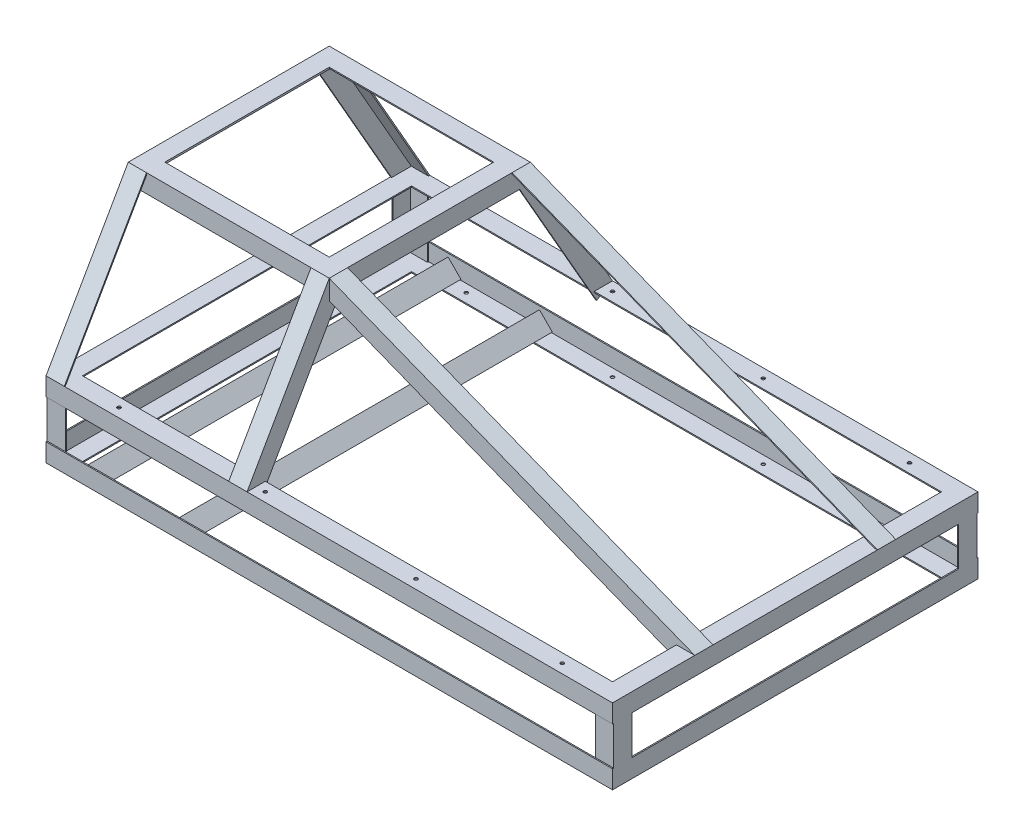
SolidWorks part; units mm, degrees
material "6061 Alloy"
ref_plane "Front Plane" through (0, 0, 0) normal (0, 0, 1) x (1, 0, 0)
ref_plane "Top Plane" through (0, 0, 0) normal (0, 1, 0) x (1, 0, 0)
ref_plane "Right Plane" through (0, 0, 0) normal (1, 0, 0) x (0, 0, -1)
sketch "Sketch2" plane through (0, 0, 0) normal (1, 0, 0) x (0, 0, -1)
  line L0 (-504.825, -346.075) -> (-504.825, -422.275)
  line L1 (504.825, -422.275) -> (-504.825, -422.275) construction
  line L2 (504.825, -422.275) -> (504.825, 422.275) construction
  line L3 (504.825, 422.275) -> (-504.825, 422.275) construction
  line L4 (-504.825, -422.275) -> (-504.825, 422.275) construction
  line L5 (504.825, -422.275) -> (-504.825, 422.275) construction
  line L6 (504.825, 422.275) -> (-504.825, -422.275) construction
  line L7 (-504.825, -422.275) -> (-428.625, -422.275)
  line L8 (-428.625, -422.275) -> (-428.625, -417.195)
  line L9 (-428.625, -417.195) -> (-498.7519, -417.195)
  line L10 (-498.7519, -417.195) -> (-498.7519, -346.075)
  line L11 (-498.7519, -346.075) -> (-504.825, -346.075)
  line L12 (0, 0) -> (0, -148.4726) construction
  line L13 (0, 0) -> (158.633, 0) construction
  line L14 (498.7519, -417.195) -> (498.7519, -346.075)
  line L15 (428.625, -417.195) -> (498.7519, -417.195)
  line L16 (428.625, -422.275) -> (428.625, -417.195)
  line L17 (504.825, -422.275) -> (428.625, -422.275)
  line L18 (504.825, -346.075) -> (504.825, -422.275)
  line L19 (498.7519, -346.075) -> (504.825, -346.075)
  line L20 (428.625, 417.195) -> (498.7519, 417.195)
  line L21 (428.625, 422.275) -> (428.625, 417.195)
  line L22 (504.825, 422.275) -> (428.625, 422.275)
  line L23 (504.825, 346.075) -> (504.825, 422.275)
  line L24 (498.7519, 346.075) -> (504.825, 346.075)
  line L25 (498.7519, 417.195) -> (498.7519, 346.075)
  line L26 (-498.7519, 417.195) -> (-498.7519, 346.075)
  line L27 (-428.625, 417.195) -> (-498.7519, 417.195)
  line L28 (-428.625, 422.275) -> (-428.625, 417.195)
  line L29 (-504.825, 422.275) -> (-428.625, 422.275)
  line L30 (-504.825, 346.075) -> (-504.825, 422.275)
  line L31 (-498.7519, 346.075) -> (-504.825, 346.075)
  point P0 (0, 0)
  dimension "D1" = 1009.65
  dimension "D2" = 844.55
  dimension "D3" = 76.2
  dimension "D4" = 5.08
extrude "OAL Lenth" [suppressed] add sketch "Sketch2" along normal blind 1574.8
sketch "Sketch3" [suppressed] plane through (0, 0, 0) normal (0, 0, 1) x (1, 0, 0)
  line L0 (0, -422.275) -> (0, -346.075)
  line L1 (1574.8, -346.075) -> (0, -346.075) construction
  line L2 (0, -346.075) -> (0, -422.275) construction
  line L3 (0, -346.075) -> (5.08, -346.075)
  line L4 (5.08, -346.075) -> (5.08, -417.195)
  line L5 (5.08, -417.195) -> (76.2, -417.195)
  line L6 (76.2, -417.195) -> (76.2, -422.275)
  line L7 (1574.8, -422.275) -> (0, -422.275) construction
  line L8 (76.2, -422.275) -> (0, -422.275)
  line L9 (0, 0) -> (697.1877, 0) construction
  line L10 (787.4, 346.075) -> (787.4, -346.075) construction
  line L11 (1574.8, 346.075) -> (0, 346.075) construction
  line L12 (76.2, 422.275) -> (0, 422.275)
  line L13 (76.2, 417.195) -> (76.2, 422.275)
  line L14 (5.08, 417.195) -> (76.2, 417.195)
  line L15 (5.08, 346.075) -> (5.08, 417.195)
  line L16 (0, 346.075) -> (5.08, 346.075)
  line L17 (0, 422.275) -> (0, 346.075)
  line L18 (1574.8, 422.275) -> (1574.8, 346.075)
  line L19 (1574.8, 346.075) -> (1569.72, 346.075)
  line L20 (1569.72, 346.075) -> (1569.72, 417.195)
  line L21 (1569.72, 417.195) -> (1498.6, 417.195)
  line L22 (1498.6, 417.195) -> (1498.6, 422.275)
  line L23 (1498.6, 422.275) -> (1574.8, 422.275)
  line L24 (1498.6, -422.275) -> (1574.8, -422.275)
  line L25 (1498.6, -417.195) -> (1498.6, -422.275)
  line L26 (1569.72, -417.195) -> (1498.6, -417.195)
  line L27 (1569.72, -346.075) -> (1569.72, -417.195)
  line L28 (1574.8, -346.075) -> (1569.72, -346.075)
  line L29 (1574.8, -422.275) -> (1574.8, -346.075)
  dimension "D1" = 5.08
extrude "OAL Width" [suppressed] add sketch "Sketch3" along normal up to surface and the other way up to surface
sketch "Sketch4" [suppressed] plane through (0, 422.275, 0) normal (0, 1, 0) x (1, 0, 0)
  line L0 (0, 504.825) -> (0, 428.625)
  line L1 (0, -428.625) -> (0, -504.825) construction
  line L2 (0, 428.625) -> (5.08, 428.625)
  line L3 (5.08, 428.625) -> (5.08, 499.745)
  line L4 (5.08, 499.745) -> (76.2, 499.745)
  line L5 (76.2, 499.745) -> (76.2, 504.825)
  line L6 (0, 504.825) -> (1574.8, 504.825) construction
  line L7 (76.2, 504.825) -> (0, 504.825)
  line L8 (0, 0) -> (1574.8, 0) construction
  line L9 (1574.8, -428.625) -> (1574.8, -504.825) construction
  line L10 (787.4, 0) -> (787.4, 504.825) construction
  line L11 (76.2, -504.825) -> (0, -504.825)
  line L12 (76.2, -499.745) -> (76.2, -504.825)
  line L13 (5.08, -499.745) -> (76.2, -499.745)
  line L14 (5.08, -428.625) -> (5.08, -499.745)
  line L15 (0, -428.625) -> (5.08, -428.625)
  line L16 (0, -504.825) -> (0, -428.625)
  line L17 (1574.8, -504.825) -> (1574.8, -428.625)
  line L18 (1574.8, -428.625) -> (1569.72, -428.625)
  line L19 (1569.72, -428.625) -> (1569.72, -499.745)
  line L20 (1569.72, -499.745) -> (1498.6, -499.745)
  line L21 (1498.6, -499.745) -> (1498.6, -504.825)
  line L22 (1498.6, -504.825) -> (1574.8, -504.825)
  line L23 (1498.6, 504.825) -> (1574.8, 504.825)
  line L24 (1498.6, 499.745) -> (1498.6, 504.825)
  line L25 (1569.72, 499.745) -> (1498.6, 499.745)
  line L26 (1569.72, 428.625) -> (1569.72, 499.745)
  line L27 (1574.8, 428.625) -> (1569.72, 428.625)
  line L28 (1574.8, 504.825) -> (1574.8, 428.625)
  dimension "D1" = 5.08
  dimension "D2" = 76.2
extrude "OAL Height" [suppressed] add sketch "Sketch4" against normal through all
sketch "Sketch5" plane through (0, 0, 0) normal (1, 0, 0) x (0, 0, -1)
  line L0 (0, 304.8) -> (0, -304.8) construction
  line L1 (-508, -304.8) -> (508, -304.8) construction
  line L2 (-508, -304.8) -> (-508, -254)
  line L3 (-508, -304.8) -> (-457.2, -304.8)
  line L4 (-457.2, -304.8) -> (-457.2, -301.625)
  line L5 (-457.2, -301.625) -> (-504.825, -301.625)
  line L6 (-504.825, -301.625) -> (-504.825, -254)
  line L7 (-504.825, -254) -> (-508, -254)
  line L8 (504.825, -254) -> (508, -254)
  line L9 (504.825, -301.625) -> (504.825, -254)
  line L10 (457.2, -301.625) -> (504.825, -301.625)
  line L11 (457.2, -304.8) -> (457.2, -301.625)
  line L12 (508, -304.8) -> (457.2, -304.8)
  line L13 (508, -304.8) -> (508, -254)
  line L14 (0, -200.025) -> (-176.3903, -200.025) construction
  line L15 (-508, -95.25) -> (508, -95.25) construction
  line L16 (508, -95.25) -> (508, -146.05)
  line L17 (508, -95.25) -> (457.2, -95.25)
  line L18 (457.2, -95.25) -> (457.2, -98.425)
  line L19 (457.2, -98.425) -> (504.825, -98.425)
  line L20 (504.825, -98.425) -> (504.825, -146.05)
  line L21 (504.825, -146.05) -> (508, -146.05)
  line L22 (-504.825, -146.05) -> (-508, -146.05)
  line L23 (-504.825, -98.425) -> (-504.825, -146.05)
  line L24 (-457.2, -98.425) -> (-504.825, -98.425)
  line L25 (-457.2, -95.25) -> (-457.2, -98.425)
  line L26 (-508, -95.25) -> (-457.2, -95.25)
  line L27 (-508, -95.25) -> (-508, -146.05)
  point P4 (0, 0)
  point P8 (0, -304.8)
  point P32 (0, -95.25)
  dimension "D1" = 1016
  dimension "D2" = 609.6
  dimension "D3" = 50.8
  dimension "D4" = 3.175
  dimension "D5" = 104.775
extrude "Bottom Horizontal Angle" add sketch "Sketch5" along normal blind 1574.8 separate body
sketch "Sketch6" plane through (0, -304.8, 0) normal (0, -1, 0) x (1, 0, 0)
  line L0 (0, 0) -> (1574.8, 0) construction
  line L1 (1574.8, -504.825) -> (1574.8, 504.825) construction
  line L2 (1574.8, -504.825) -> (1524, -504.825)
  line L3 (1574.8, -504.825) -> (1574.8, -454.025)
  line L4 (1574.8, -454.025) -> (1571.625, -454.025)
  line L5 (1571.625, -454.025) -> (1571.625, -501.65)
  line L6 (1571.625, -501.65) -> (1524, -501.65)
  line L7 (1524, -501.65) -> (1524, -504.825)
  line L8 (1524, 501.65) -> (1524, 504.825)
  line L9 (1571.625, 501.65) -> (1524, 501.65)
  line L10 (1571.625, 454.025) -> (1571.625, 501.65)
  line L11 (1574.8, 454.025) -> (1571.625, 454.025)
  line L12 (1574.8, 504.825) -> (1574.8, 454.025)
  line L13 (1574.8, 504.825) -> (1524, 504.825)
  line L15 (787.4, 0) -> (787.4, 197.6325) construction
  line L16 (0, -504.825) -> (0, 504.825) construction
  line L17 (0, 504.825) -> (50.8, 504.825)
  line L18 (0, 504.825) -> (0, 454.025)
  line L19 (0, 454.025) -> (3.175, 454.025)
  line L20 (3.175, 454.025) -> (3.175, 501.65)
  line L21 (3.175, 501.65) -> (50.8, 501.65)
  line L22 (50.8, 501.65) -> (50.8, 504.825)
  line L23 (50.8, -501.65) -> (50.8, -504.825)
  line L24 (3.175, -501.65) -> (50.8, -501.65)
  line L25 (3.175, -454.025) -> (3.175, -501.65)
  line L26 (0, -454.025) -> (3.175, -454.025)
  line L27 (0, -504.825) -> (0, -454.025)
  line L28 (0, -504.825) -> (50.8, -504.825)
  point P3 (787.4, 0)
  point P6 (1574.8, 0)
  point P32 (0, 0)
  dimension "D1" = 50.8
  dimension "D2" = 3.175
  dimension "D3" = 1009.65
  dimension "D4" = 1574.8
extrude "Front Vertial Angle" add sketch "Sketch6" against normal blind 209.55
sketch "Sketch12" plane through (0, 0, 0) normal (-1, 0, 0) x (0, 0, 1)
  line L0 (0, -304.8) -> (0, 304.8) construction
  line L1 (0, -304.8) -> (-454.025, -304.8) construction
  line L2 (-279.4, 304.8) -> (279.4, 304.8) construction
  line L3 (279.4, 304.8) -> (508, -95.25)
  line L4 (508, -95.25) -> (322.1581, -95.25)
  line L5 (454.025, -95.25) -> (508, -95.25) construction
  line L6 (508, -95.25) -> (508, -146.05) construction
  point P9 (0, 304.8)
  dimension "D1" = 609.6
  dimension "D2" = 558.8
ref_plane "Plane2" through (0, -95.25, 508) normal (0, -0.8682, 0.4961) x (-1, 0, 0)
sketch "Sketch13" plane through (0, -95.25, 508) normal (0, -0.8682, 0.4961) x (-1, 0, 0)
  line L0 (0, 0) -> (0, 50.8)
  line L1 (0, 485.1743) -> (0, 0) construction
  line L2 (0, 50.8) -> (-3.175, 50.8)
  line L3 (-3.175, 50.8) -> (-3.175, 3.175)
  line L4 (-3.175, 3.175) -> (-50.8, 3.175)
  line L5 (-50.8, 3.175) -> (-50.8, 0)
  line L6 (-1574.8, 0) -> (0, 0) construction
  line L7 (-50.8, 0) -> (0, 0)
  line L8 (0, 0) -> (-558.8, 0) construction
  line L9 (-279.4, 0) -> (-279.4, -79.7814) construction
  line L10 (-508, 0) -> (-558.8, 0)
  line L11 (-508, 3.175) -> (-508, 0)
  line L12 (-555.625, 3.175) -> (-508, 3.175)
  line L13 (-555.625, 50.8) -> (-555.625, 3.175)
  line L14 (-558.8, 50.8) -> (-555.625, 50.8)
  line L15 (-558.8, 0) -> (-558.8, 50.8)
  line L16 (-1574.8, 0) -> (0, 0) construction
  dimension "D1" = 3.175
  dimension "D2" = 50.8
  dimension "D3" = 558.8
extrude "Rear Diagonal Angle" add sketch "Sketch13" against normal up to vertex (460.758 mm away) up to point (0, 304.8, 279.4)
sketch "Sketch14" plane through (0, 0, 0) normal (0, 0, 1) x (1, 0, 0)
  line L1 (0, 304.8) -> (0, -95.25) construction
  line L2 (0, -95.25) -> (558.8, -95.25) construction
  line L3 (279.4, -95.25) -> (279.4, 65.0322) construction
  line L4 (553.72, 254) -> (558.8, 254)
  line L5 (558.8, 254) -> (558.8, 304.8)
  line L6 (558.8, 304.8) -> (508, 304.8)
  line L12 (508, 304.8) -> (508, 299.72)
  line L13 (508, 299.72) -> (553.72, 299.72)
  line L26 (5.08, 299.72) -> (5.08, 254)
  line L27 (50.8, 299.72) -> (5.08, 299.72)
  line L28 (50.8, 304.8) -> (50.8, 299.72)
  line L29 (0, 304.8) -> (50.8, 304.8)
  line L30 (0, 254) -> (0, 304.8)
  line L31 (5.08, 254) -> (0, 254)
  line L32 (553.72, 299.72) -> (553.72, 254)
  dimension "D1" = 50.8
  dimension "D2" = 5.08
extrude "Rear Top Angle" add sketch "Sketch14" along normal up to next
sketch "Sketch7" plane through (0, -304.8, 0) normal (0, -1, 0) x (1, 0, 0)
  line L0 (609.6, 0) -> (0, 0) construction
  line L1 (0, 504.825) -> (0, -504.825) construction
  line L2 (0, 504.825) -> (50.8, 504.825)
  line L3 (0, 504.825) -> (0, 454.025)
  line L4 (0, 454.025) -> (3.175, 454.025)
  line L5 (3.175, 454.025) -> (3.175, 501.65)
  line L6 (3.175, 501.65) -> (50.8, 501.65)
  line L7 (50.8, 501.65) -> (50.8, 504.825)
  line L8 (50.8, -501.65) -> (50.8, -504.825)
  line L9 (3.175, -501.65) -> (50.8, -501.65)
  line L10 (3.175, -454.025) -> (3.175, -501.65)
  line L11 (0, -454.025) -> (3.175, -454.025)
  line L12 (0, -504.825) -> (0, -454.025)
  line L13 (0, -504.825) -> (50.8, -504.825)
  point P3 (304.8, 0)
  point P6 (0, 0)
extrude "Rear Vertical Angle" [suppressed] add sketch "Sketch7" against normal blind 609.6
sketch "Sketch8" plane through (0, 0, 0) normal (-1, 0, 0) x (0, 0, 1)
  line L0 (0, -304.8) -> (0, 304.8) construction
  line L2 (279.4, 304.8) -> (279.4, 254)
  line L3 (279.4, 304.8) -> (228.6, 304.8)
  line L4 (228.6, 304.8) -> (228.6, 301.625)
  line L5 (228.6, 301.625) -> (276.225, 301.625)
  line L6 (276.225, 301.625) -> (276.225, 254)
  line L7 (276.225, 254) -> (279.4, 254)
  point P3 (0, 0)
  point P6 (0, 304.8)
extrude "Rear Top Horizontal Angle" add sketch "Sketch8" against normal up to surface (558.8 mm away) up to face at (558.8, 67.7551, 324.2285)
sketch "Sketch15" plane through (0, 0, 508) normal (0, 0, 1) x (1, 0, 0)
  line L0 (0, -254) -> (0, -304.8)
  line L1 (0, -95.25) -> (1574.8, -95.25) construction
  line L2 (787.4, -95.25) -> (787.4, 43.9233) construction
  line L3 (1571.625, -254) -> (1574.8, -254)
  line L4 (1571.625, -301.625) -> (1571.625, -254)
  line L5 (1524, -301.625) -> (1571.625, -301.625)
  line L6 (1524, -304.8) -> (1524, -301.625)
  line L7 (0, -304.8) -> (50.8, -304.8)
  line L8 (50.8, -304.8) -> (50.8, -301.625)
  line L9 (50.8, -301.625) -> (3.175, -301.625)
  line L10 (3.175, -301.625) -> (3.175, -254)
  line L11 (3.175, -254) -> (0, -254)
  line L12 (1574.8, -304.8) -> (1524, -304.8)
  line L13 (1574.8, -254) -> (1574.8, -304.8)
  line L20 (787.4, -95.25) -> (787.4, -304.8) construction
  line L21 (1574.8, -304.8) -> (0, -304.8) construction
  line L24 (787.4, -200.025) -> (896.4031, -200.025) construction
  line L27 (1574.8, -146.05) -> (1574.8, -95.25)
  line L28 (1574.8, -95.25) -> (1524, -95.25)
  line L29 (1524, -95.25) -> (1524, -98.425)
  line L30 (1524, -98.425) -> (1571.625, -98.425)
  line L31 (1571.625, -98.425) -> (1571.625, -146.05)
  line L32 (1571.625, -146.05) -> (1574.8, -146.05)
  line L33 (18.8814, -200.025) -> (113.1502, -200.025) construction
  line L35 (3.175, -146.05) -> (0, -146.05)
  line L36 (3.175, -98.425) -> (3.175, -146.05)
  line L37 (50.8, -98.425) -> (3.175, -98.425)
  line L38 (50.8, -95.25) -> (50.8, -98.425)
  line L39 (0, -95.25) -> (50.8, -95.25)
  line L40 (0, -146.05) -> (0, -95.25)
  dimension "D1" = 50.8
  dimension "D2" = 3.175
extrude "Boss-Extrude9" add sketch "Sketch15" against normal up to surface (508 mm away)
mirror "Mirror3" about plane through (0, 0, 0) normal (0, 0, 1)
sketch "Top Center Angle Plane" plane through (0, 0, 508) normal (0, 0, 1) x (1, 0, 0)
  line L0 (558.8, 304.8) -> (1574.8, -95.25)
  line L1 (558.8, 304.8) -> (509.3836, 179.2981)
ref_plane "Top Front Diagonal Angle PLane" through (379.8876, -149.5807, 0) normal (0.9305, -0.3664, 0) x (0, 0, -1)
sketch "Sketch10" plane through (379.8876, -149.5807, 0) normal (0.9305, -0.3664, 0) x (0, 0, -1)
  line L0 (-279.4, 488.3354) -> (279.4, 488.3354) construction
  line L1 (279.4, 488.3354) -> (-279.4, 488.3354) construction
  line L8 (-276.225, 437.5354) -> (-279.4, 437.5354)
  line L9 (-276.225, 485.1604) -> (-276.225, 437.5354)
  line L10 (-228.6, 485.1604) -> (-276.225, 485.1604)
  line L11 (-228.6, 488.3354) -> (-228.6, 485.1604)
  line L12 (-279.4, 488.3354) -> (-228.6, 488.3354)
  line L13 (-279.4, 488.3354) -> (-279.4, 437.5354)
  line L14 (0, 488.3354) -> (0, 449.1208) construction
  line L15 (279.4, 488.3354) -> (279.4, 437.5354)
  line L16 (279.4, 488.3354) -> (228.6, 488.3354)
  line L17 (228.6, 488.3354) -> (228.6, 485.1604)
  line L18 (228.6, 485.1604) -> (276.225, 485.1604)
  line L19 (276.225, 485.1604) -> (276.225, 437.5354)
  line L20 (276.225, 437.5354) -> (279.4, 437.5354)
  point P4 (0, 119.046)
  point P8 (0, 488.3354)
  dimension "D1" = 279.4
  dimension "D2" = 50.8
  dimension "D5" = 3.175
extrude "Top Front Diagonal Angle" add sketch "Sketch10" along normal up to vertex
sketch "Sketch11" [suppressed] plane through (0, 0, -504.825) normal (0, 0, -1) x (-1, 0, 0)
  line L0 (0, -101.6) -> (-1574.8, -101.6) construction
  line L1 (-1574.8, 101.6) -> (-1574.8, -304.8) construction
  line L2 (-1574.8, 101.6) -> (-1524, 101.6)
  line L3 (-1574.8, 101.6) -> (-1574.8, 50.8)
  line L4 (-1574.8, 50.8) -> (-1571.625, 50.8)
  line L5 (-1571.625, 50.8) -> (-1571.625, 98.425)
  line L6 (-1571.625, 98.425) -> (-1524, 98.425)
  line L7 (-1524, 98.425) -> (-1524, 101.6)
  line L8 (-1524, -301.625) -> (-1524, -304.8)
  line L9 (-1571.625, -301.625) -> (-1524, -301.625)
  line L10 (-1571.625, -254) -> (-1571.625, -301.625)
  line L11 (-1574.8, -254) -> (-1571.625, -254)
  line L12 (-1574.8, -304.8) -> (-1574.8, -254)
  line L13 (-1574.8, -304.8) -> (-1524, -304.8)
  line L14 (0, -304.8) -> (-50.8, -304.8)
  line L15 (-50.8, -301.625) -> (-50.8, -304.8)
  line L16 (-3.175, -254) -> (-3.175, -301.625)
  line L17 (0, -254) -> (-3.175, -254)
  line L18 (0, -304.8) -> (0, -254)
  line L19 (-3.175, -301.625) -> (-50.8, -301.625)
  line L20 (0, 0) -> (-419.4352, 0) construction
  line L21 (-3.175, 301.625) -> (-50.8, 301.625)
  line L22 (0, 304.8) -> (0, 254)
  line L23 (0, 254) -> (-3.175, 254)
  line L24 (-3.175, 254) -> (-3.175, 301.625)
  line L25 (-50.8, 301.625) -> (-50.8, 304.8)
  line L26 (0, 304.8) -> (-50.8, 304.8)
  line L27 (-605.3402, 263.2815) -> (-644.7354, 295.3543)
  line L28 (-605.3402, 263.2815) -> (-573.2675, 302.6767)
  line L29 (-642.7308, 297.8165) -> (-644.7354, 295.3543)
  line L30 (-605.7978, 267.7483) -> (-642.7308, 297.8165)
  line L31 (-573.2675, 302.6767) -> (-575.7297, 304.6813)
  line L32 (-575.7297, 304.6813) -> (-605.7978, 267.7483)
  line L33 (-643.7056, 301.2489) -> (-575.4944, 308.3511) construction
  line L38 (-643.7056, 301.2489) -> (-643.3359, 297.6977) construction
  line L40 (-575.4944, 308.3511) -> (-575.1246, 304.8) construction
  line L42 (0, 304.8) -> (-609.6, 304.8) construction
  line L43 (-1574.8, 101.6) -> (-609.6, 304.8) construction
  line L44 (-643.3359, 297.6977) -> (-575.1246, 304.8) construction
  line L45 (-609.2302, 301.2489) -> (-606.0734, 270.9299) construction
  line L46 (-642.7977, 298.5481) -> (-575.6628, 303.9496) construction
  line L47 (-609.2302, 301.2489) -> (-605.7978, 267.7483) construction
  point P3 (-787.4, -101.6)
  point P6 (-1574.8, -101.6)
  point P47 (-609.6, 304.8)
  point P51 (-575.4944, 308.3511)
  dimension "D1" = 50.8
  dimension "D2" = 3.175
  dimension "D3" = 68.58
extrude "Top Center Angle" [suppressed] add sketch "Sketch11" against normal through all
sketch "Sketch16" plane through (0, 0, 504.825) normal (0, 0, -1) x (-1, 0, 0)
  line L0 (-394.696, -299.0624) -> (-358.775, -263.1414)
  line L1 (-1524, -301.625) -> (-50.8, -301.625) construction
  line L2 (-358.775, -263.1414) -> (-322.854, -299.0624)
  line L4 (-322.854, -299.0624) -> (-325.099, -301.3075)
  line L5 (-325.099, -301.3075) -> (-358.775, -267.6315)
  line L6 (-358.775, -267.6315) -> (-392.451, -301.3075)
  line L7 (-392.451, -301.3075) -> (-394.696, -299.0624)
  line L8 (-392.451, -301.3075) -> (-325.099, -301.3075) construction
  line L9 (-358.775, -263.1414) -> (-358.775, -267.6315) construction
  line L10 (-358.775, -267.6315) -> (-358.775, -301.3075) construction
  line L12 (-3.175, -98.425) -> (-3.175, -301.625) construction
  line L13 (-138.451, -301.3075) -> (-140.696, -299.0624)
  line L14 (-140.696, -299.0624) -> (-104.775, -263.1414)
  line L15 (-104.775, -263.1414) -> (-68.854, -299.0624)
  line L16 (-68.854, -299.0624) -> (-71.099, -301.3075)
  line L17 (-71.099, -301.3075) -> (-104.775, -267.6315)
  line L18 (-104.775, -267.6315) -> (-138.451, -301.3075)
  dimension "D1" = 50.8
  dimension "D2" = 3.175
  dimension "D3" = 355.6
  dimension "D5" = 0.3175
  dimension "D4" = 2
extrude "Boss-Extrude14" add sketch "Sketch16" along normal up to next
sketch "Wheel Reference" plane through (0, 0, 0) normal (0, 0, 1) x (1, 0, 0)
  line L0 (1409.7, -317.5) -> (1003.3, -317.5) construction
  line L1 (1003.3, -317.5) -> (584.2, -317.5) construction
  line L2 (584.2, -317.5) -> (177.8, -317.5) construction
  line L3 (1409.7, -317.5) -> (1574.8, -317.5) construction
  line L4 (1574.8, -317.5) -> (1574.8, -304.8) construction
  line L5 (1574.8, -146.05) -> (1574.8, -254) construction
  line L6 (1524, -304.8) -> (50.8, -304.8) construction
  circle A0 centre (1409.7, -317.5) radius 190.5
  circle A1 centre (1003.3, -317.5) radius 190.5
  circle A2 centre (584.2, -317.5) radius 190.5
  circle A3 centre (177.8, -317.5) radius 190.5
  point P8 (1409.7, -508)
  point P12 (1574.8, -304.8)
  point P15 (1600.2, -317.5)
  dimension "D1" = 381
  dimension "D2" = 406.4
  dimension "D3" = 419.1
  dimension "D4" = 12.7
  dimension "D5" = 165.1
  dimension "D6" = 25.4
  dimension "D7" = 203.2
sketch "Sketch18" plane through (0, 0, 0) normal (0, 1, 0) x (1, 0, 0)
  line L0 (1409.7, 0) -> (1409.7, 482.6) construction
  line L1 (1574.8, 508) -> (558.8, 508) construction
  line L2 (1003.3, 0) -> (1003.3, 482.6) construction
  line L3 (1003.3, 0) -> (584.2, 0) construction
  line L4 (1409.7, 0) -> (1003.3, 0) construction
  line L5 (584.2, 0) -> (584.2, 482.6) construction
  line L6 (584.2, 0) -> (177.8, 0) construction
  line L7 (177.8, 0) -> (177.8, 482.6) construction
  line L8 (-12.7, 0) -> (368.3, 0) construction
  line L10 (177.8, 482.6) -> (584.2, 482.6) construction
  line L11 (584.2, 482.6) -> (1003.3, 482.6) construction
  line L12 (1003.3, 482.6) -> (1409.7, 482.6) construction
  line L13 (1409.7, 0) -> (1845.1924, 0) construction
  line L14 (1003.3, -482.6) -> (1409.7, -482.6) construction
  line L15 (584.2, -482.6) -> (1003.3, -482.6) construction
  line L16 (177.8, -482.6) -> (584.2, -482.6) construction
  circle A0 centre (1409.7, 482.6) radius 4.7625
  circle A1 centre (1003.3, 482.6) radius 4.7625
  circle A2 centre (584.2, 482.6) radius 4.7625
  circle A3 centre (177.8, 482.6) radius 4.7625
  circle A4 centre (177.8, -482.6) radius 4.7625
  circle A5 centre (584.2, -482.6) radius 4.7625
  circle A6 centre (1003.3, -482.6) radius 4.7625
  circle A7 centre (1409.7, -482.6) radius 4.7625
  dimension "D2" = 9.525
  dimension "D1" = 25.4
extrude "Wheel Mount LOC" cut sketch "Sketch18" against normal through all both and the other way through all
sketch "Sketch20" plane through (0, 0, 0) normal (0, 0, 1) x (1, 0, 0)
  line L0 (1574.8, -254) -> (1574.8, -304.8)
  line L1 (1574.8, -304.8) -> (1524, -304.8)
  line L2 (1524, -304.8) -> (1524, -292.1)
  line L3 (1524, -254) -> (1524, -301.625) construction
  line L4 (1524, -292.1) -> (1537.8673, -254)
  line L5 (1537.8673, -254) -> (1574.8, -254)
  line L6 (1533.5236, -265.9341) -> (1395.5095, -215.7011) construction
  dimension "D1" = 20
  dimension "D2" = 12.7
  dimension "D3" = 12.7
sketch "Sketch21" plane through (0, 0, 0) normal (0, 0, 1) x (1, 0, 0)
  line L0 (1570.5391, -280.7513) -> (1537.7203, -268.8062)
  line L1 (1571.625, -98.425) -> (1571.625, -301.625) construction
  line L2 (1537.7203, -268.8062) -> (1525.7753, -301.625)
  line L3 (1524, -301.625) -> (50.8, -301.625) construction
  line L4 (1525.7753, -301.625) -> (1522.7917, -300.5391)
  line L5 (1522.7917, -300.5391) -> (1535.8227, -264.7368)
  line L6 (1535.8227, -264.7368) -> (1571.625, -277.7678)
  line L8 (1571.625, -277.7678) -> (1570.5391, -280.7513)
  line L9 (1524, -254) -> (1524, -301.625) construction
  point P10 (1539.0407, -267.9848)
  dimension "D1" = 3.175
  dimension "D2" = 38.1
  dimension "D3" = 20
